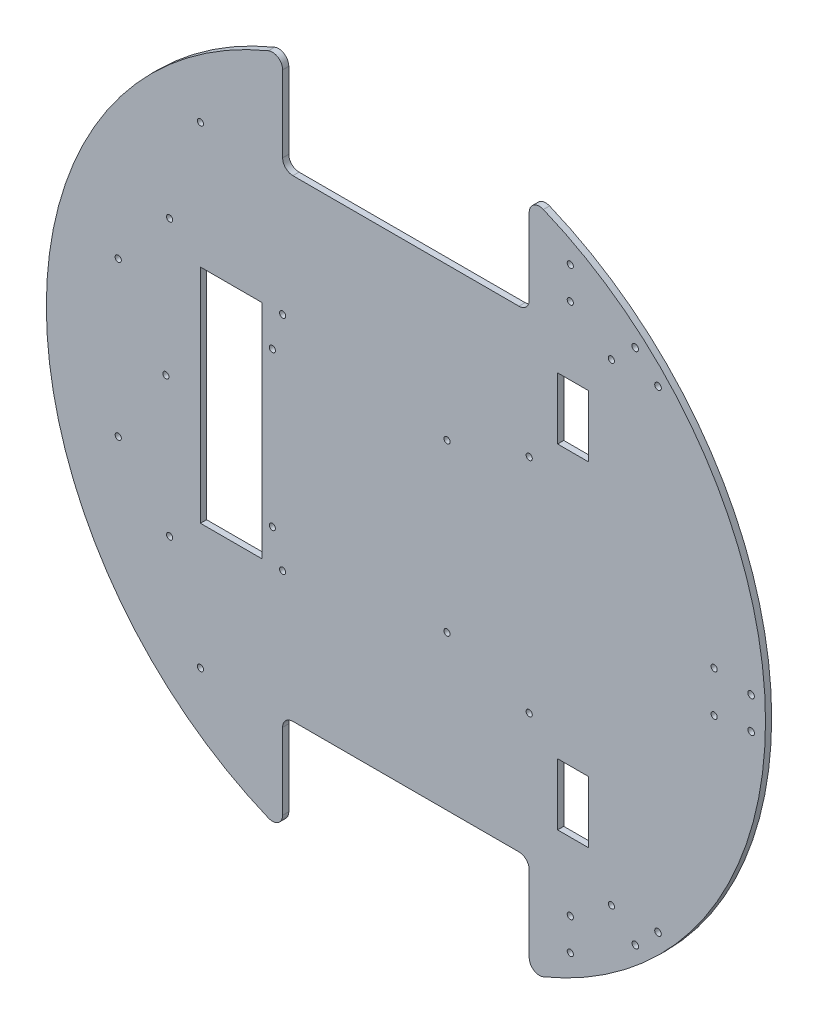
SolidWorks part; units mm, degrees
material "ｱｸﾘﾙ (中-上級の耐衝撃性)"
ref_plane "正面" through (0, 0, 0) normal (0, 0, 1) x (1, 0, 0)
ref_plane "平面" through (0, 0, 0) normal (0, 1, 0) x (1, 0, 0)
ref_plane "右側面" through (0, 0, 0) normal (1, 0, 0) x (0, 0, -1)
sketch "ｽｹｯﾁ1" plane through (0, 0, 0) normal (0, 0, 1) x (1, 0, 0)
  circle A0 centre (0, 0) radius 175
  dimension "D1" = 350
extrude "ﾎﾞｽ - 押し出し1" add sketch "ｽｹｯﾁ1" along normal blind 3
sketch "ｽｹｯﾁ2" plane through (0, 0, 3) normal (0, 0, 1) x (1, 0, 0)
  line L0 (0, 0) -> (175, 0)
  line L1 (0, 0) -> (-175, 0)
  line L2 (0, 0) -> (0, 115)
  line L3 (0, 0) -> (0, -115)
  line L4 (0, 115) -> (60, 115)
  line L5 (0, 115) -> (0, 175)
  line L6 (0, 175) -> (60, 175)
  line L7 (60, 115) -> (60, 175)
  line L8 (0, 115) -> (-60, 115)
  line L9 (0, 115) -> (0, 175)
  line L10 (0, 175) -> (-60, 175)
  line L11 (-60, 115) -> (-60, 175)
  line L13 (0, -115) -> (60, -115)
  line L14 (0, -115) -> (0, -175)
  line L15 (0, -175) -> (60, -175)
  line L16 (60, -115) -> (60, -175)
  line L17 (0, -115) -> (-60, -115)
  line L18 (0, -115) -> (0, -175)
  line L19 (0, -175) -> (-60, -175)
  line L20 (-60, -115) -> (-60, -175)
  circle A0 centre (0, 0) radius 175 construction
  circle M1 centre (0, 0) radius 175
  dimension "D1" = 115
  dimension "D2" = 60
  dimension "D3" = 60
  dimension "D4" = 60
  dimension "D5" = 115
  dimension "D6" = 60
extrude "ｶｯﾄ - 押し出し1" cut sketch "ｽｹｯﾁ2" against normal blind 3 contours L11 L8 L5 M1 | L4 L7 L5 M1 | L17 L20 L14 M1 | L16 L13 L14 M1
fillet "ﾌｨﾚｯﾄ1" radius 5 1 edges at (-60, 164.3928, 1.5)
fillet "ﾌｨﾚｯﾄ2" radius 5 3 edges at (60, 115, 1.5) (60, 164.3928, 1.5) (-60, 115, 1.5)
fillet "ﾌｨﾚｯﾄ3" radius 5 4 edges at (-60, -164.3928, 1.5) (-60, -115, 1.5) (60, -164.3928, 1.5) (60, -115, 1.5)
sketch "ｽｹｯﾁ5" plane through (0, 0, 3) normal (0, 0, 1) x (1, 0, 0)
  line L0 (0, 115) -> (-100, 115)
  line L1 (55, 115) -> (-55, 115) construction
  line L2 (0, 115) -> (100, 115)
  line L3 (0, -115) -> (100, -115)
  line L4 (55, -115) -> (-55, -115) construction
  line L5 (100, -115) -> (-100, -115)
  circle A0 centre (-100, -115) radius 1.5
  circle A1 centre (100, -115) radius 1.5
  circle A2 centre (100, 115) radius 1.5
  circle A3 centre (-100, 115) radius 1.5
  dimension "D3" = 3
  dimension "D4" = 3
  dimension "D5" = 3
  dimension "D6" = 3
  dimension "D1" = 100
  dimension "D2" = 100
extrude "ｶｯﾄ - 押し出し4" cut sketch "ｽｹｯﾁ5" against normal blind 3 contours A1 | A0 | A3 | A2
sketch "ｽｹｯﾁ6" plane through (0, 0, 3) normal (0, 0, 1) x (1, 0, 0)
  line L1 (-60, 54) -> (60, 54)
  line L2 (-60, 54) -> (-60, -54)
  line L3 (-60, -54) -> (60, -54)
  line L4 (60, 54) -> (60, -54)
  line L5 (-60, 54) -> (60, -54) construction
  line L6 (-60, -54) -> (60, 54) construction
  circle A0 centre (-60, 54) radius 1.5
  circle A1 centre (60, 54) radius 1.5
  circle A2 centre (-60, -54) radius 1.5
  circle A3 centre (60, -54) radius 1.5
  point P0 (0, 0)
  dimension "D3" = 3
  dimension "D4" = 3
  dimension "D5" = 3
  dimension "D6" = 3
  dimension "D1" = 120
  dimension "D2" = 108
extrude "ｶｯﾄ - 押し出し5" cut sketch "ｽｹｯﾁ6" against normal blind 3 contours A2 | A0 | A1 | A3
sketch "ｽｹｯﾁ7" plane through (0, 0, 3) normal (0, 0, 1) x (1, 0, 0)
  line L0 (-60, -54) -> (-70, -54)
  line L2 (-70, -54) -> (-100, -54)
  line L3 (-70, -54) -> (-70, 54)
  line L4 (-70, 54) -> (-100, 54)
  line L5 (-100, -54) -> (-100, 54)
  dimension "D1" = 10
  dimension "D2" = 108
  dimension "D3" = 30
extrude "ｶｯﾄ - 押し出し6" cut sketch "ｽｹｯﾁ7" against normal blind 3 contours L5 L2 L3 L4
sketch "ｽｹｯﾁ8" plane through (0, 0, 3) normal (0, 0, 1) x (1, 0, 0)
  line L0 (-100, 0) -> (-115, 0)
  line L1 (-100, -54) -> (-100, 54) construction
  line L2 (-115, 0) -> (-115, 67)
  line L3 (-115, 0) -> (-115, -67)
  circle A0 centre (-115, -67) radius 1.5
  circle A1 centre (-116.8225, 0) radius 1.5
  circle A2 centre (-115, 67) radius 1.5
  dimension "D4" = 3
  dimension "D5" = 3
  dimension "D6" = 3
  dimension "D1" = 15
  dimension "D2" = 67
  dimension "D3" = 67
extrude "ｶｯﾄ - 押し出し7" cut sketch "ｽｹｯﾁ8" against normal blind 3 contours A2 | A1 | A0
sketch "ｽｹｯﾁ9" plane through (0, 0, 3) normal (0, 0, 1) x (1, 0, 0)
  line L0 (-70, 0) -> (-65, 0)
  line L1 (-70, -54) -> (-70, 54) construction
  line L2 (-65, 0) -> (-65, 37)
  line L3 (-65, 37) -> (-64.7716, 37.1905)
  line L4 (-65, 0) -> (-65, -38)
  line L5 (-65, 0) -> (20, 0)
  line L6 (20, 0) -> (20, 41)
  line L7 (20, 0) -> (20, -40)
  circle A0 centre (-65, 37) radius 1.5
  circle A1 centre (20, 41) radius 1.5
  circle A2 centre (-65, -38) radius 1.5
  circle A3 centre (20, -40) radius 1.5
  dimension "D7" = 3
  dimension "D8" = 3
  dimension "D9" = 3
  dimension "D10" = 3
  dimension "D1" = 5
  dimension "D2" = 37
  dimension "D3" = 38
  dimension "D4" = 85
  dimension "D5" = 41
  dimension "D6" = 40
extrude "ｶｯﾄ - 押し出し8" cut sketch "ｽｹｯﾁ9" against normal blind 10 contours A0 | A2 | A1 | A3
sketch "ｽｹｯﾁ10" plane through (0, 0, 3) normal (0, 0, 1) x (1, 0, 0)
  line L0 (0, 0) -> (152.2366, 0)
  line L1 (0, 0) -> (66.9742, 68.8711)
  line L2 (0, 0) -> (76.2283, -78.3873)
  line L3 (175, 0) -> (168, 0)
  line L4 (-175, 0) -> (-168, 0)
  line L5 (66.9742, 68.8711) -> (117.1237, 120.441)
  line L6 (76.2283, -78.3873) -> (117.1237, -120.441)
  line L7 (117.1237, -120.441) -> (122.6798, -115.038)
  line L8 (117.1237, -120.441) -> (111.6437, -125.9211)
  line L9 (168, 0) -> (168, 7.75)
  line L10 (168, 0) -> (168, -7.75)
  line L11 (117.1237, 120.441) -> (111.5677, 125.844)
  line L12 (117.1237, 120.441) -> (122.6798, 115.038)
  arc A0 (66.9118, -161.7029) -> (66.9118, 161.7029) centre (0, 0) ccw construction
  arc A1 (-66.9118, 161.7029) -> (-66.9118, -161.7029) centre (0, 0) ccw construction
  circle A2 centre (0, 0) radius 168
  circle A3 centre (111.6437, -125.9211) radius 1.6
  circle A4 centre (122.6798, -115.038) radius 1.6
  circle A5 centre (168, 7.75) radius 1.6
  circle A6 centre (168, -7.75) radius 1.6
  circle A7 centre (111.5677, 125.844) radius 1.6
  circle A8 centre (122.6798, 115.038) radius 1.6
  dimension "D7" = 3.2
  dimension "D8" = 3.2
  dimension "D11" = 3.2
  dimension "D12" = 3.2
  dimension "D15" = 3.2
  dimension "D16" = 3.2
  dimension "D1" = 45.8
  dimension "D2" = 45.8
  dimension "D3" = 7
  dimension "D4" = 7
  dimension "D5" = 7.75
  dimension "D6" = 7.75
  dimension "D9" = 7.75
  dimension "D10" = 7.75
  dimension "D13" = 7.75
  dimension "D14" = 7.75
extrude "ｶｯﾄ - 押し出し9" cut sketch "ｽｹｯﾁ10" against normal blind 10 contours A3 | A4 | A6 | A5 | A7 | A8
sketch "ｽｹｯﾁ11" plane through (0, 0, 3) normal (0, 0, 1) x (1, 0, 0)
  line L0 (0, 0) -> (115, 0)
  line L1 (0, 0) -> (81.3173, 81.3173)
  line L2 (0, 0) -> (81.3173, -81.3173)
  line L4 (73.8173, 96.3173) -> (88.8173, 96.3173)
  line L5 (73.8173, 96.3173) -> (73.8173, 66.3173)
  line L6 (73.8173, 66.3173) -> (88.8173, 66.3173)
  line L7 (88.8173, 96.3173) -> (88.8173, 66.3173)
  line L8 (73.8173, 96.3173) -> (88.8173, 66.3173) construction
  line L9 (73.8173, 66.3173) -> (88.8173, 96.3173) construction
  line L10 (73.8173, -66.3173) -> (88.8173, -66.3173)
  line L11 (73.8173, -66.3173) -> (73.8173, -96.3173)
  line L12 (73.8173, -96.3173) -> (88.8173, -96.3173)
  line L13 (88.8173, -66.3173) -> (88.8173, -96.3173)
  line L14 (73.8173, -66.3173) -> (88.8173, -96.3173) construction
  line L15 (73.8173, -96.3173) -> (88.8173, -66.3173) construction
  circle A0 centre (0, 0) radius 115
  dimension "D1" = 230
  dimension "D2" = 45
  dimension "D3" = 45
  dimension "D4" = 30
  dimension "D5" = 15
  dimension "D6" = 15
  dimension "D7" = 30
extrude "ｶｯﾄ - 押し出し10" cut sketch "ｽｹｯﾁ11" against normal blind 10 contours L7 L6 L5 L4 | L13 L12 L11 L10
sketch "ｽｹｯﾁ16" plane through (0, 0, 3) normal (0, 0, 1) x (1, 0, 0)
ref_plane "平面8" through (0, 0, 10) normal (0, 0, 1) x (1, 0, 0)
sketch "ｽｹｯﾁ20" plane through (0, 0, 10) normal (0, 0, 1) x (1, 0, 0)
  line L0 (0, 0) -> (-214.2919, 0) construction
  line L1 (0, 0) -> (199.1346, 0) construction
  line L2 (0, 0) -> (0, 188.9427) construction
  line L3 (0, 0) -> (0, -234.9711) construction
sketch "ｽｹｯﾁ22" plane through (0, 0, 10) normal (0, 0, 1) x (1, 0, 0)
  line L0 (0, 0) -> (199.1346, 0) construction
  line L1 (0, 0) -> (0, -234.9711) construction
  circle A0 centre (150, -10) radius 1.5
  circle A1 centre (150, 10) radius 1.5
  dimension "D1" = 3
  dimension "D2" = 3
  dimension "D4" = 10
  dimension "D3" = 10
  dimension "D5" = 150
  dimension "D6" = 150
extrude "ｶｯﾄ - 押し出し11" cut sketch "ｽｹｯﾁ22" against normal blind 10
sketch "ｽｹｯﾁ23" plane through (0, 0, 3) normal (0, 0, 1) x (1, 0, 0)
  line L0 (0, 0) -> (0, 188.9427) construction
  line L1 (0, 0) -> (0, -234.9711) construction
  line L2 (0, 0) -> (199.1346, 0) construction
  line L3 (0, 0) -> (-214.2919, 0) construction
  circle A0 centre (80, 145) radius 1.5
  circle A1 centre (80, 129.5) radius 1.5
  circle A2 centre (80, -129.5) radius 1.5
  circle A3 centre (80, -145) radius 1.5
  circle A4 centre (-140, 37.5) radius 1.5
  circle A5 centre (-140, -37.5) radius 1.5
  dimension "D1" = 3
  dimension "D2" = 3
  dimension "D5" = 3
  dimension "D6" = 3
  dimension "D13" = 3
  dimension "D14" = 3
  dimension "D3" = 80
  dimension "D4" = 80
  dimension "D7" = 80
  dimension "D8" = 80
  dimension "D9" = 129.5
  dimension "D10" = 145
  dimension "D11" = 129.5
  dimension "D12" = 145
  dimension "D15" = 37.5
  dimension "D16" = 37.5
  dimension "D17" = 140
  dimension "D18" = 140
extrude "ｶｯﾄ - 押し出し12" cut sketch "ｽｹｯﾁ23" against normal blind 10
